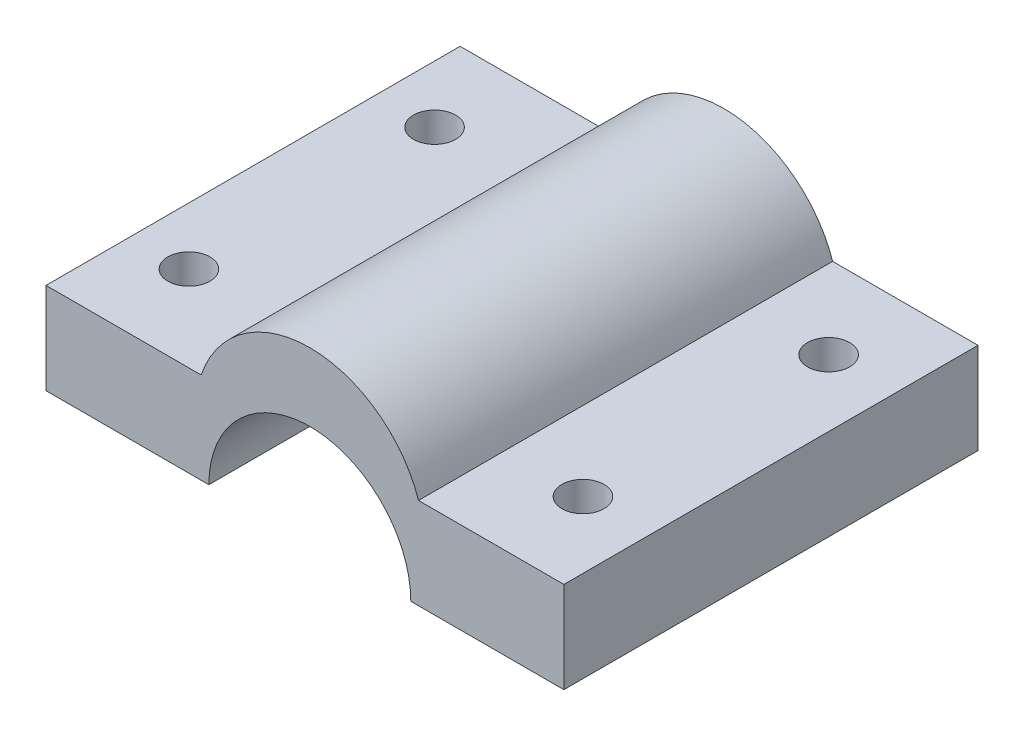
SolidWorks part; units mm, degrees
ref_plane "Front Plane" through (0, 0, 0) normal (0, 0, 1) x (1, 0, 0)
ref_plane "Top Plane" through (0, 0, 0) normal (0, 1, 0) x (1, 0, 0)
ref_plane "Right Plane" through (0, 0, 0) normal (1, 0, 0) x (0, 0, -1)
sketch "Sketch1" plane through (0, 0, 0) normal (0, 0, 1) x (1, 0, 0)
  line L0 (-9.5162, -14.7473) -> (8.0353, -14.7473)
  line L1 (-54.4932, -25.7586) -> (-34.8301, -25.7586)
  line L2 (-54.4932, -25.7586) -> (-54.4932, -14.7473)
  line L3 (-54.4932, -14.7473) -> (-35.7619, -14.7473)
  line L4 (8.0353, -25.7586) -> (8.0353, -14.7473)
  line L5 (-10.448, -25.7586) -> (8.0353, -25.7586)
  arc A0 (-35.7619, -14.7473) -> (-9.5162, -14.7473) centre (-22.6391, -19.1819) cw
  arc A1 (-34.8301, -25.7586) -> (-10.448, -25.7586) centre (-22.6391, -25.7586) cw
extrude "Boss-Extrude1" add sketch "Sketch1" along normal blind 50
sketch "Sketch2" plane through (0, 0, 0) normal (0, 1, 0) x (1, 0, 0)
  circle A0 centre (-47.5771, -10.0037) radius 2.5455
  circle A1 centre (0, -10.0037) radius 2.5455
  circle A2 centre (0, -39.6642) radius 2.5455
  circle A3 centre (-47.5771, -39.6642) radius 2.5455
extrude "Cut-Extrude1" cut sketch "Sketch2" against normal blind 50
